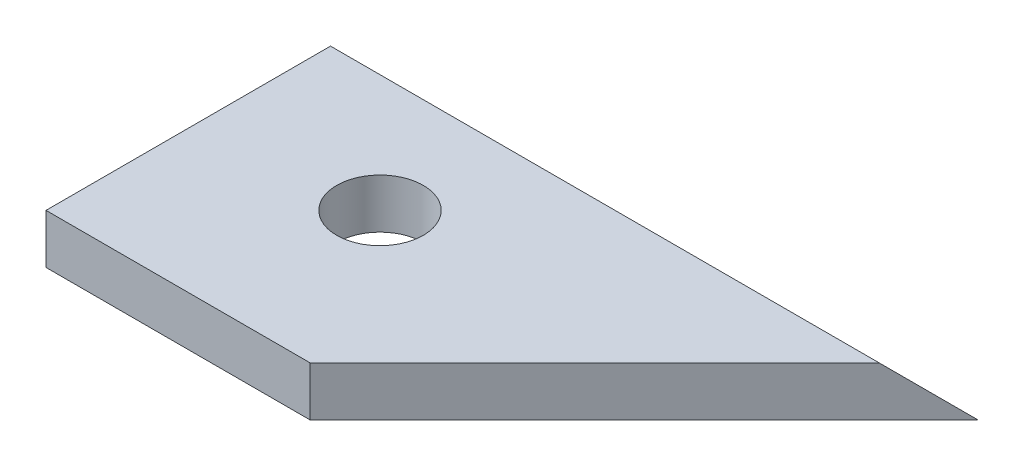
SolidWorks part; units mm, degrees
ref_plane "Front Plane" through (0, 0, 0) normal (0, 0, 1) x (1, 0, 0)
ref_plane "Top Plane" through (0, 0, 0) normal (0, 1, 0) x (1, 0, 0)
ref_plane "Right Plane" through (0, 0, 0) normal (1, 0, 0) x (0, 0, -1)
sketch "Sketch1" plane through (0, 0, 0) normal (0, 1, 0) x (1, 0, 0)
  line L0 (0, -21.7136) -> (54, 32.2864)
  line L1 (-42.6863, 32.2864) -> (11.3137, 32.2864)
  line L2 (-42.6863, 32.2864) -> (-42.6863, -21.7136)
  line L3 (-42.6863, -21.7136) -> (0, -21.7136)
  line L5 (-42.6863, 5.2864) -> (11.3137, 5.2864) construction
  line L9 (11.3137, 32.2864) -> (54, 32.2864)
  circle A0 centre (-15.6863, 5.2864) radius 7
  dimension "D3" = 27
  dimension "D1" = 54
  dimension "D2" = 42.6863
  dimension "D4" = 96.6863
extrude "Boss-Extrude1" add sketch "Sketch1" along normal blind 8
sketch "Sketch4" plane through (0, 0, 0) normal (1, 0, 0) x (0, 0, -1)
  line L0 (32.2864, 0) -> (24.2864, 8)
  line L1 (-21.7136, 8) -> (32.2864, 8) construction
  line L2 (24.2864, 8) -> (32.2864, 8)
  line L3 (32.2864, 8) -> (32.2864, 0)
extrude "Cut-Extrude4" cut sketch "Sketch4" along normal blind 192 from surface at -42.6863 starting at face at (-42.6863, 4, -5.2864)
